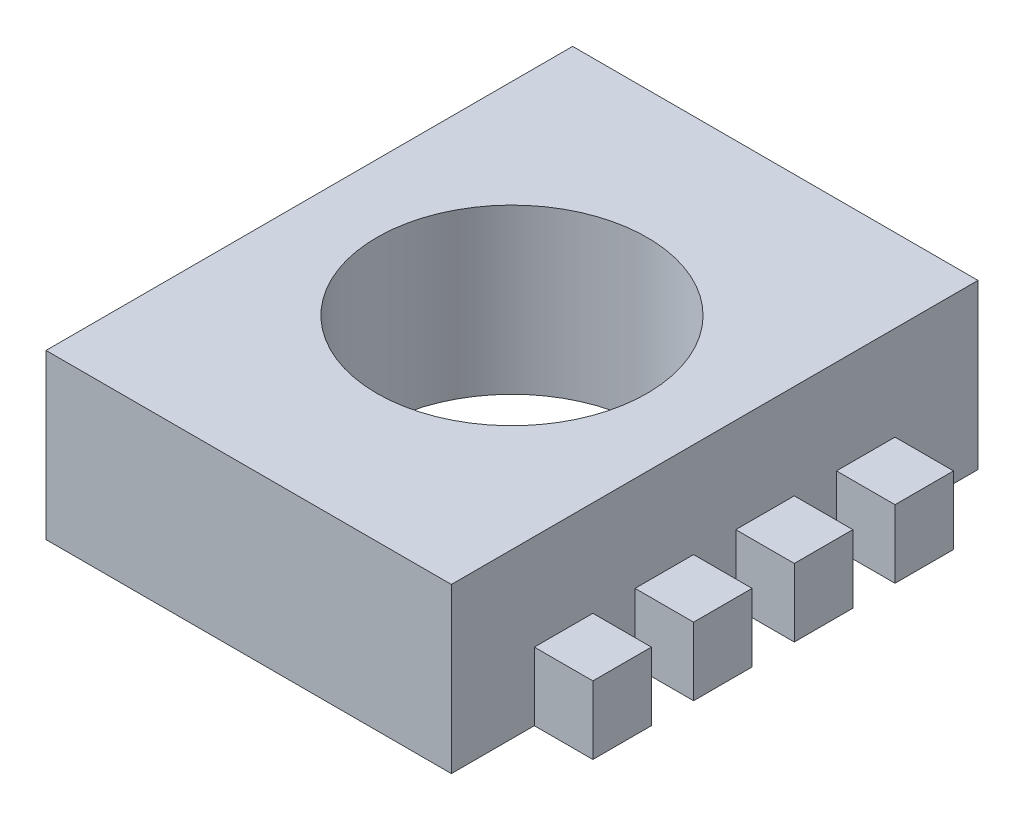
SolidWorks part; units mm, degrees
ref_plane "Front Plane" through (0, 0, 0) normal (0, 0, 1) x (1, 0, 0)
ref_plane "Top Plane" through (0, 0, 0) normal (0, 1, 0) x (1, 0, 0)
ref_plane "Right Plane" through (0, 0, 0) normal (1, 0, 0) x (0, 0, -1)
sketch "Sketch1" plane through (0, 0, 0) normal (0, 1, 0) x (1, 0, 0)
  line L1 (-1.905, -2.475) -> (1.905, -2.475)
  line L2 (-1.905, -2.475) -> (-1.905, 2.475)
  line L3 (-1.905, 2.475) -> (1.905, 2.475)
  line L4 (1.905, -2.475) -> (1.905, 2.475)
  line L5 (-1.905, -2.475) -> (1.905, 2.475) construction
  line L6 (-1.905, 2.475) -> (1.905, -2.475) construction
  circle A0 centre (0, 0) radius 1.27
  point P0 (0, 0)
  dimension "D3" = 2.54
  dimension "D1" = 4.95
  dimension "D2" = 3.81
extrude "Boss-Extrude1" add sketch "Sketch1" along normal blind 1.54
sketch "Sketch2" plane through (1.905, 0, 0) normal (1, 0, 0) x (0, 0, -1)
  line L0 (-2.475, 0) -> (2.475, 0) construction
  line L1 (-1.695, 0.64) -> (-1.145, 0.64)
  line L2 (-1.695, 0.64) -> (-1.695, 0)
  line L3 (-1.695, 0) -> (-1.145, 0)
  line L4 (-1.145, 0.64) -> (-1.145, 0)
  line L5 (-1.695, 0.64) -> (-1.145, 0) construction
  line L6 (-1.695, 0) -> (-1.145, 0.64) construction
  line L7 (-0.7483, 0.6447) -> (-0.1983, 0.6447)
  line L8 (-0.7483, 0.6447) -> (-0.7483, 0.0047)
  line L9 (-0.1983, 0.6447) -> (-0.1983, 0.0047)
  line L10 (-0.7483, 0.0047) -> (-0.1983, 0.0047)
  line L11 (0.1983, 0.6495) -> (0.7483, 0.6495)
  line L12 (0.1983, 0.6495) -> (0.1983, 0.0095)
  line L13 (0.7483, 0.6495) -> (0.7483, 0.0095)
  line L14 (0.1983, 0.0095) -> (0.7483, 0.0095)
  line L15 (1.145, 0.6542) -> (1.695, 0.6542)
  line L16 (1.145, 0.6542) -> (1.145, 0.0142)
  line L17 (1.695, 0.6542) -> (1.695, 0.0142)
  line L18 (1.145, 0.0142) -> (1.695, 0.0142)
  point P0 (-1.42, 0.32)
  point P7 (0, 0)
  point P8 (0, 0)
  dimension "D1" = 0.78
  dimension "D2" = 0.78
  dimension "D3" = 0.64
  dimension "D5" = 0.55
  dimension "D4" = 4
extrude "Boss-Extrude2" add sketch "Sketch2" along normal blind 0.55
sketch "Sketch4" plane through (-1.905, 0, 0) normal (-1, 0, 0) x (0, 0, 1)
  line L0 (-2.475, 0) -> (2.475, 0) construction
  line L1 (-1.695, 0.64) -> (-1.145, 0.64)
  line L2 (-1.695, 0.64) -> (-1.695, 0)
  line L3 (-1.695, 0) -> (-1.145, 0)
  line L4 (-1.145, 0.64) -> (-1.145, 0)
  line L5 (-1.695, 0.64) -> (-1.145, 0) construction
  line L6 (-1.695, 0) -> (-1.145, 0.64) construction
  line L7 (-0.745, 0.6401) -> (-0.745, 0.0001)
  line L8 (-0.745, 0.6401) -> (-0.195, 0.6401)
  line L9 (-0.195, 0.6401) -> (-0.195, 0.0001)
  line L10 (-0.745, 0.0001) -> (-0.195, 0.0001)
  line L11 (0.205, 0.6402) -> (0.205, 0.0002)
  line L12 (0.205, 0.6402) -> (0.755, 0.6402)
  line L13 (0.755, 0.6402) -> (0.755, 0.0002)
  line L14 (0.205, 0.0002) -> (0.755, 0.0002)
  line L15 (1.155, 0.6403) -> (1.155, 0.0003)
  line L16 (1.155, 0.6403) -> (1.705, 0.6403)
  line L17 (1.705, 0.6403) -> (1.705, 0.0003)
  line L18 (1.155, 0.0003) -> (1.705, 0.0003)
  point P0 (-1.42, 0.32)
  dimension "D1" = 0.64
  dimension "D2" = 0.55
  dimension "D3" = 0.78
  dimension "D5" = 0.4
  dimension "D4" = 4
extrude "Boss-Extrude3" add sketch "Sketch4" along normal blind 0.55
